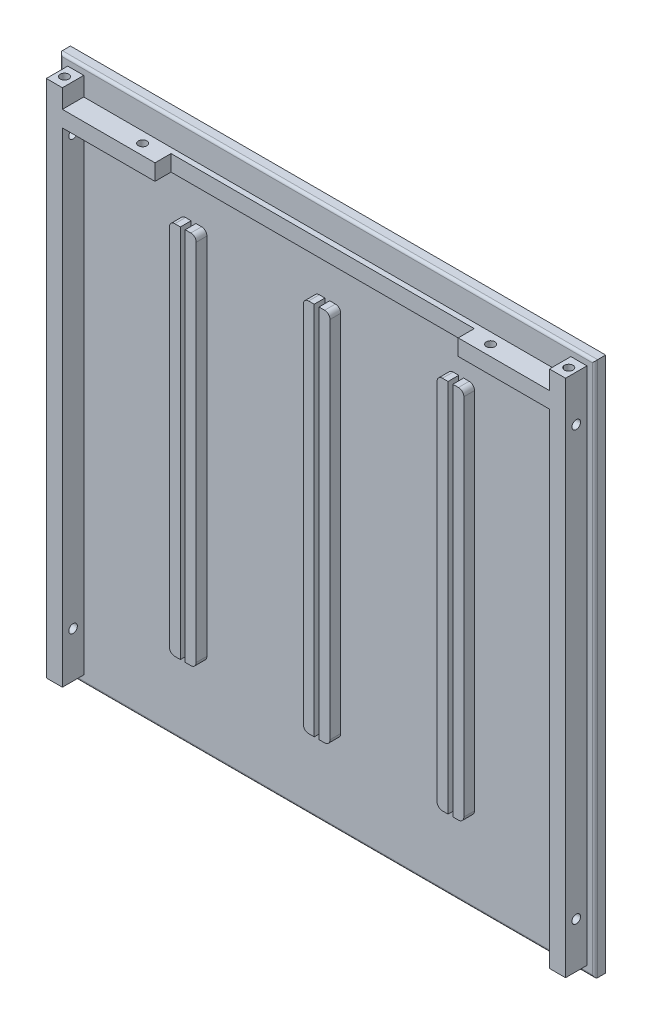
SolidWorks part; units mm, degrees
ref_plane "Plan de face" through (0, 0, 0) normal (0, 0, 1) x (1, 0, 0)
ref_plane "Plan de dessus" through (0, 0, 0) normal (0, 1, 0) x (1, 0, 0)
ref_plane "Plan de droite" through (0, 0, 0) normal (1, 0, 0) x (0, 0, -1)
sketch "Esquisse1" plane through (0, 0, 0) normal (0, 0, 1) x (1, 0, 0)
  line L1 (0, 0) -> (200, 0)
  line L2 (0, 0) -> (0, 200)
  line L3 (0, 200) -> (200, 200)
  line L4 (200, 0) -> (200, 200)
  dimension "D1" = 200
  dimension "D2" = 200
extrude "Boss.-Extru. Paroie" add sketch "Esquisse1" along normal blind 4
sketch "Esquisse2" plane through (0, 0, 4) normal (0, 0, 1) x (1, 0, 0)
  line L0 (0, 0) -> (200, 0) construction
  line L1 (47, 170) -> (53, 170)
  line L2 (45, 168) -> (45, 32)
  line L3 (47, 30) -> (53, 30)
  line L4 (55, 168) -> (55, 32)
  line L5 (0, 200) -> (0, 0) construction
  line L18 (97, 170) -> (103, 170)
  line L19 (95, 168) -> (95, 32)
  line L20 (97, 30) -> (103, 30)
  line L21 (105, 168) -> (105, 32)
  line L22 (147, 170) -> (153, 170)
  line L23 (145, 168) -> (145, 32)
  line L24 (147, 30) -> (153, 30)
  line L25 (155, 168) -> (155, 32)
  arc A0 (45, 32) -> (47, 30) centre (47, 32) ccw
  arc A1 (53, 30) -> (55, 32) centre (53, 32) ccw
  arc A2 (53, 170) -> (55, 168) centre (53, 168) cw
  arc A3 (47, 170) -> (45, 168) centre (47, 168) ccw
  arc A16 (95, 32) -> (97, 30) centre (97, 32) ccw
  arc A17 (103, 30) -> (105, 32) centre (103, 32) ccw
  arc A18 (103, 170) -> (105, 168) centre (103, 168) cw
  arc A19 (97, 170) -> (95, 168) centre (97, 168) ccw
  arc A20 (145, 32) -> (147, 30) centre (147, 32) ccw
  arc A21 (153, 30) -> (155, 32) centre (153, 32) ccw
  arc A22 (153, 170) -> (155, 168) centre (153, 168) cw
  arc A23 (147, 170) -> (145, 168) centre (147, 168) ccw
  point P10 (45, 30)
  point P15 (55, 170)
  point P18 (45, 170)
  dimension "D5" = 2
  dimension "D1" = 10
  dimension "D2" = 140
  dimension "D3" = 30
  dimension "D4" = 45
  dimension "D6" = 3
sketch "Esquisse4" plane through (0, 0, 4) normal (0, 0, 1) x (1, 0, 0)
  line L0 (3, 3) -> (9, 3)
  line L6 (0, 0) -> (200, 0) construction
  line L17 (9, 3) -> (9, 184)
  line L18 (9, 184) -> (191, 184)
  line L19 (191, 184) -> (191, 3)
  line L20 (191, 3) -> (197, 3)
  line L21 (197, 3) -> (197, 197)
  line L22 (197, 197) -> (191, 197)
  line L24 (191, 197) -> (191, 190)
  line L26 (191, 190) -> (9, 190)
  line L27 (9, 190) -> (9, 197)
  line L28 (9, 197) -> (3, 197)
  line L29 (3, 197) -> (3, 3)
  line L31 (0, 200) -> (0, 0) construction
  line L32 (200, 200) -> (0, 200) construction
  line L33 (200, 0) -> (200, 200) construction
  dimension "D1" = 6
  dimension "D2" = 3
  dimension "D3" = 3
  dimension "D4" = 6
  dimension "D5" = 6
  dimension "D6" = 3
  dimension "D7" = 3
  dimension "D8" = 6
  dimension "D9" = 3
  dimension "D10" = 10
  dimension "D11" = 3
  dimension "D12" = 6
extrude "Boss.-Extru. Bords" add sketch "Esquisse4" along normal blind 8
extrude "Boss.-Extru. Glissieres" add sketch "Esquisse2" along normal blind 4
fillet "Congé1" radius 1 4 edges at (200, 100, 4) (100, 200, 4) (0, 100, 4) (100, 0, 4)
sketch "Esquisse8" plane through (0, 0, 4) normal (0, 0, 1) x (1, 0, 0)
  line L0 (0, 200) -> (0, 0) construction
  line L1 (99.1, 175) -> (100.9, 175)
  line L2 (99.1, 175) -> (99.1, -5)
  line L3 (99.1, -5) -> (100.9, -5)
  line L4 (100.9, 175) -> (100.9, -5)
  line L5 (200, 200) -> (0, 200) construction
  line L6 (149.1, 175) -> (150.9, 175)
  line L7 (149.1, 175) -> (149.1, -5)
  line L8 (149.1, -5) -> (150.9, -5)
  line L9 (150.9, 175) -> (150.9, -5)
  line L10 (49.1, 175) -> (50.9, 175)
  line L11 (49.1, 175) -> (49.1, -5)
  line L12 (49.1, -5) -> (50.9, -5)
  line L13 (50.9, 175) -> (50.9, -5)
  dimension "D1" = 1.8
  dimension "D2" = 99.1
  dimension "D3" = 180
  dimension "D4" = 25
  dimension "D5" = 2
  dimension "D6" = 2
extrude "Enlèv. mat.-Extru.6" cut sketch "Esquisse8" along normal through all
sketch "Esquisse5" plane through (3, 0, 0) normal (-1, 0, 0) x (0, 0, 1)
  line L0 (12, 3) -> (4, 3) construction
  line L1 (12, 197) -> (4, 197) construction
  circle A0 centre (8, 180) radius 1.6
  circle A1 centre (8, 20) radius 1.6
  dimension "D1" = 17
  dimension "D2" = 17
extrude "Enlèv. mat.-Extru.2" cut sketch "Esquisse5" against normal blind 10
sketch "Esquisse6" plane through (197, 0, 0) normal (1, 0, 0) x (0, 0, -1)
  line L0 (0, 0) -> (0, 200) construction
  line L1 (-12, 197) -> (-4, 197) construction
  line L2 (-12, 3) -> (-4, 3) construction
  circle A0 centre (-8, 180) radius 1.6
  circle A1 centre (-8, 20) radius 1.6
  dimension "D1" = 8
  dimension "D2" = 3.2
  dimension "D3" = 17
  dimension "D4" = 17
extrude "Enlèv. mat.-Extru.3" cut sketch "Esquisse6" against normal blind 10
sketch "Esquisse7" plane through (0, 184, 0) normal (0, -1, 0) x (1, 0, 0)
  line L0 (9, 12) -> (191, 12) construction
  line L1 (9, 12) -> (9, 4) construction
  line L2 (50, 4) -> (50, 17.1304) construction
  line L3 (9, 4) -> (191, 4) construction
  circle A0 centre (35, 8) radius 1.6
  circle A1 centre (165, 8) radius 1.6
  dimension "D1" = 4
  dimension "D4" = 15
  dimension "D5" = 26
  dimension "D2" = 4
  dimension "D3" = 130
extrude "Enlèv. mat.-Extru.4" cut sketch "Esquisse7" against normal blind 10
sketch "Esquisse9" plane through (0, 197, 0) normal (0, 1, 0) x (1, 0, 0)
  line L0 (200, -3) -> (200, 0) construction
  line L2 (0, -3) -> (0, 0) construction
  line L4 (200, 0) -> (0, 0) construction
  circle A0 centre (194.2, -8) radius 1.6
  circle A1 centre (5.8, -8) radius 1.6
  dimension "D1" = 5.8
  dimension "D3" = 5.8
  dimension "D2" = 8
  dimension "D4" = 8
sketch "Esquisse10" plane through (0, 3, 0) normal (0, -1, 0) x (-1, 0, 0)
  circle A0 centre (-194.2, -8) radius 1.6
  circle A1 centre (-5.8, -8) radius 1.6
extrude "Enlèv. mat.-Extru.8" cut sketch "Esquisse10" against normal blind 10
sketch "Esquisse11" plane through (0, 0, 12) normal (0, 0, 1) x (1, 0, 0)
  line L0 (191, 190) -> (9, 190) construction
  line L1 (156.9004, 190) -> (43.5972, 190)
  line L2 (156.9004, 190) -> (156.9004, 184)
  line L3 (156.9004, 184) -> (43.5972, 184)
  line L4 (43.5972, 190) -> (43.5972, 184)
  line L5 (9, 184) -> (191, 184) construction
extrude "Enlèv. mat.-Extru.9" cut sketch "Esquisse11" against normal blind 6
extrude "Enlèv. mat.-Extru.10" cut sketch "Esquisse9" against normal blind 10
